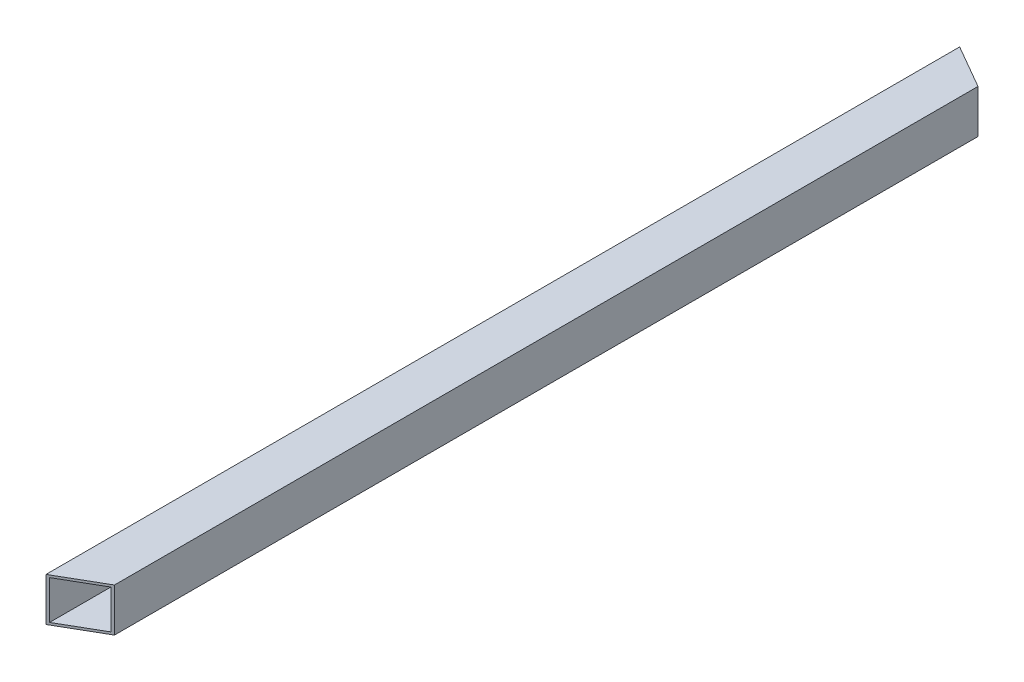
SolidWorks part; units mm, degrees
material "6061 Alloy"
ref_plane "Front Plane" through (0, 0, 0) normal (0, 0, 1) x (1, 0, 0)
ref_plane "Top Plane" through (0, 0, 0) normal (0, 1, 0) x (1, 0, 0)
ref_plane "Right Plane" through (0, 0, 0) normal (1, 0, 0) x (0, 0, -1)
sketch "Sketch1" plane through (0, 0, 0) normal (0, 0, 1) x (1, 0, 0)
  line L1 (-9.5, 9.5) -> (9.5, 9.5)
  line L2 (-9.5, 9.5) -> (-9.5, -9.5)
  line L3 (-9.5, -9.5) -> (9.5, -9.5)
  line L4 (9.5, 9.5) -> (9.5, -9.5)
  line L5 (-9.5, 9.5) -> (9.5, -9.5) construction
  line L6 (-9.5, -9.5) -> (9.5, 9.5) construction
  line L7 (-8.5, 8.5) -> (8.5, 8.5)
  line L8 (-8.5, 8.5) -> (-8.5, -8.5)
  line L9 (-8.5, -8.5) -> (8.5, -8.5)
  line L10 (8.5, 8.5) -> (8.5, -8.5)
  line L11 (-8.5, 8.5) -> (8.5, -8.5) construction
  line L12 (-8.5, -8.5) -> (8.5, 8.5) construction
  point P0 (0, 0)
  point P6 (0, 0)
  dimension "D1" = 19
  dimension "D2" = 19
  dimension "D3" = 1
extrude "Boss-Extrude1" add sketch "Sketch1" along normal blind 400
sketch "Sketch2" plane through (0, -9.5, 0) normal (0, -1, 0) x (1, 0, 0)
  line L0 (-9.5, 0) -> (9.5, 10.9697)
  line L1 (9.5, 400) -> (9.5, 0) construction
  line L2 (-9.5, 400) -> (-9.5, 0) construction
  dimension "D1" = 60
extrude "Cut-Extrude3" cut sketch "Sketch2" against normal through all and the other way through all flip side to cut
sketch "Sketch3" plane through (0, -9.5, 0) normal (0, -1, 0) x (-1, 0, 0)
  line L0 (9.5, -400) -> (-9.5, -389.0303)
  line L1 (-9.5, -400) -> (-9.5, -10.9697) construction
  line L2 (9.5, -400) -> (9.5, 0) construction
  dimension "D1" = 60
extrude "Cut-Extrude4" cut sketch "Sketch3" against normal through all and the other way through all
